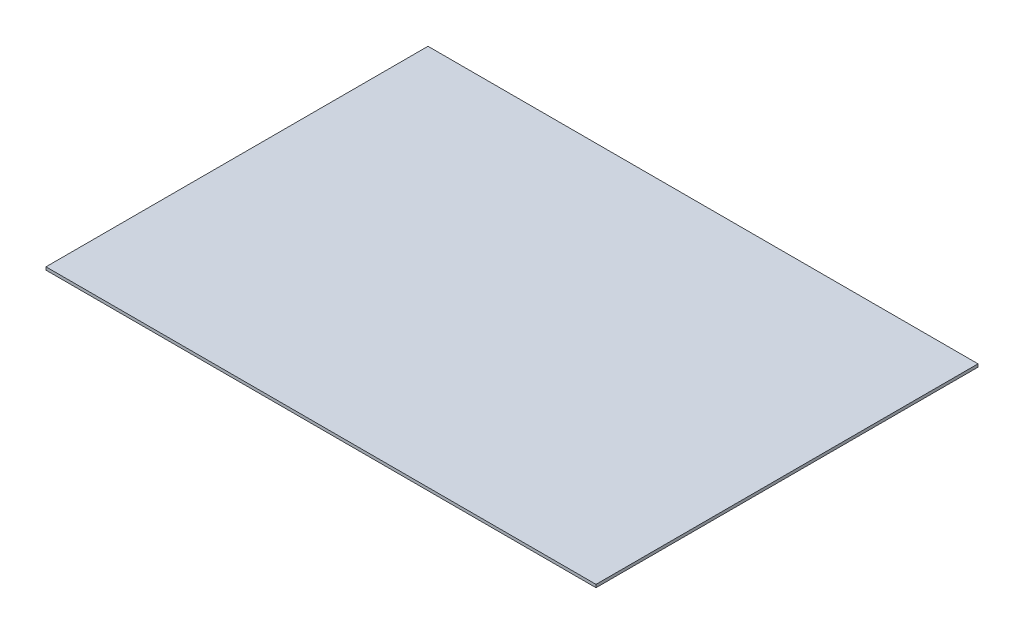
SolidWorks part; units mm, degrees
material "ABS"
ref_plane "Front Plane" through (0, 0, 0) normal (0, 0, 1) x (1, 0, 0)
ref_plane "Top Plane" through (0, 0, 0) normal (0, 1, 0) x (1, 0, 0)
ref_plane "Right Plane" through (0, 0, 0) normal (1, 0, 0) x (0, 0, -1)
sketch "Sketch1" plane through (0, 0, 0) normal (0, 0, 1) x (1, 0, 0)
  line L1 (0, 0) -> (561.55, 0)
  line L2 (0, 0) -> (0, 3)
  line L3 (0, 3) -> (561.55, 3)
  line L4 (561.55, 0) -> (561.55, 3)
  dimension "D1" = 561.55
  dimension "D2" = 3
extrude "Boss-Extrude1" add sketch "Sketch1" along normal blind 390
